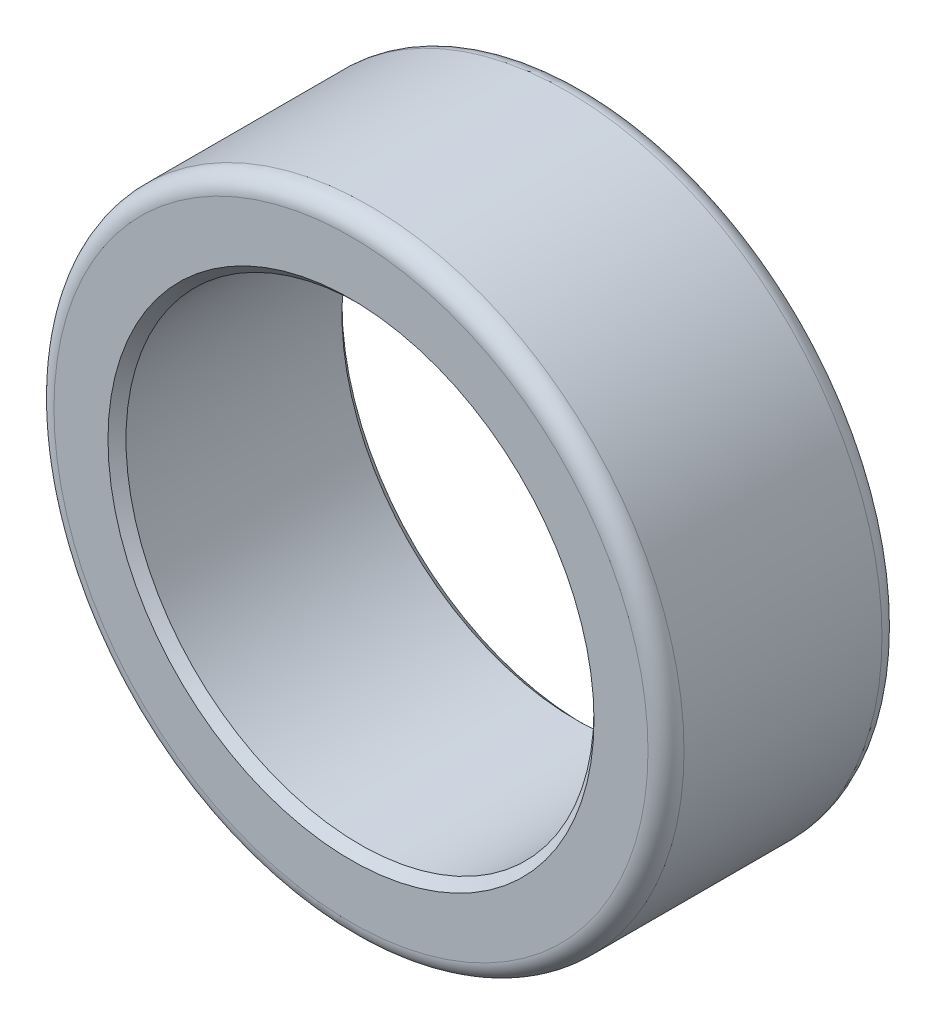
SolidWorks part; units mm, degrees
ref_plane "Alzado" through (0, 0, 0) normal (0, 0, 1) x (1, 0, 0)
ref_plane "Planta" through (0, 0, 0) normal (0, 1, 0) x (1, 0, 0)
ref_plane "Vista lateral" through (0, 0, 0) normal (1, 0, 0) x (0, 0, -1)
sketch "Croquis1" plane through (0, 0, 0) normal (0, 1, 0) x (1, 0, 0)
  line L0 (0, 0) -> (0, 50000) construction
  line L1 (0, 0) -> (26, 0) construction
  line L2 (0, 0) -> (35, 0) construction
  line L3 (26, -12) -> (26, 12)
  line L4 (26, 12) -> (27, 12) construction
  line L5 (27, 12) -> (27, 13) construction
  line L6 (27, 13) -> (33, 13)
  line L7 (35, -11) -> (35, 11)
  line L8 (26, 12) -> (27, 13)
  line L9 (35, 11) -> (33, 11) construction
  line L10 (26, -12) -> (27, -13)
  line L11 (27, -13) -> (33, -13)
  arc A0 (33, 13) -> (35, 11) centre (33, 11) cw
  arc A1 (33, -13) -> (35, -11) centre (33, -11) ccw
  point P9 (26, 0)
  point P15 (35, 0)
revolve "Revolución1" add sketch "Croquis1" angle 360 about L0
